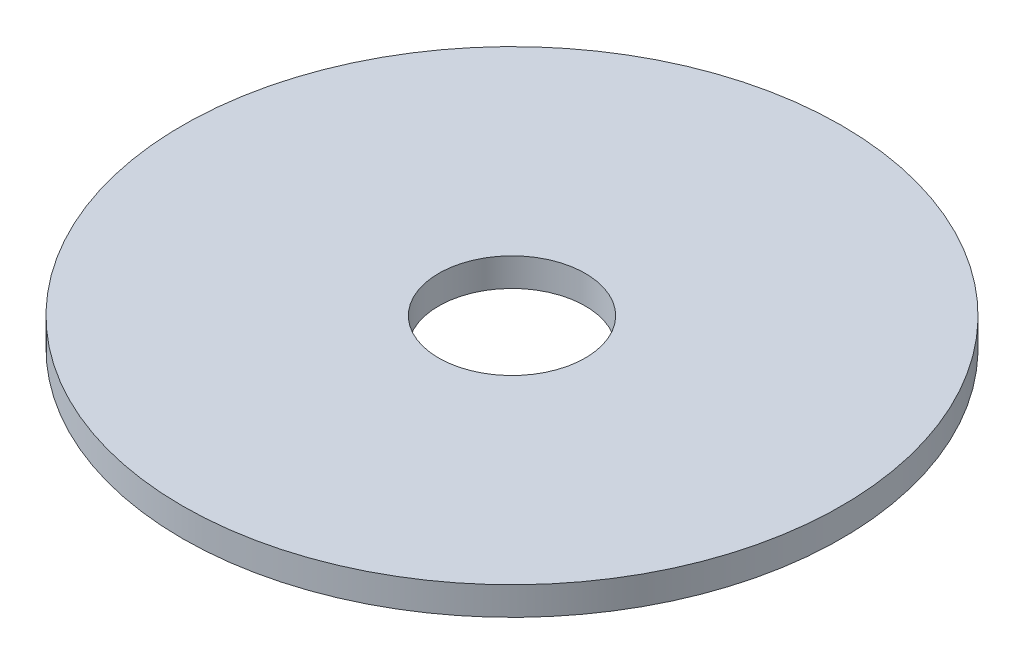
SolidWorks part; units mm, degrees
ref_plane "Front Plane" through (0, 0, 0) normal (0, 0, 1) x (1, 0, 0)
ref_plane "Top Plane" through (0, 0, 0) normal (0, 1, 0) x (1, 0, 0)
ref_plane "Right Plane" through (0, 0, 0) normal (1, 0, 0) x (0, 0, -1)
sketch "Sketch1" plane through (0, 0, 0) normal (0, 1, 0) x (1, 0, 0)
  circle A0 centre (0, 0) radius 41.5
  circle A1 centre (0, 0) radius 186.5
  dimension "D1" = 373
  dimension "D2" = 83
extrude "Boss-Extrude1" add sketch "Sketch1" along normal blind 16
scale "Scale1" scale about centroid uniform scaling yes scale factor 0.1
